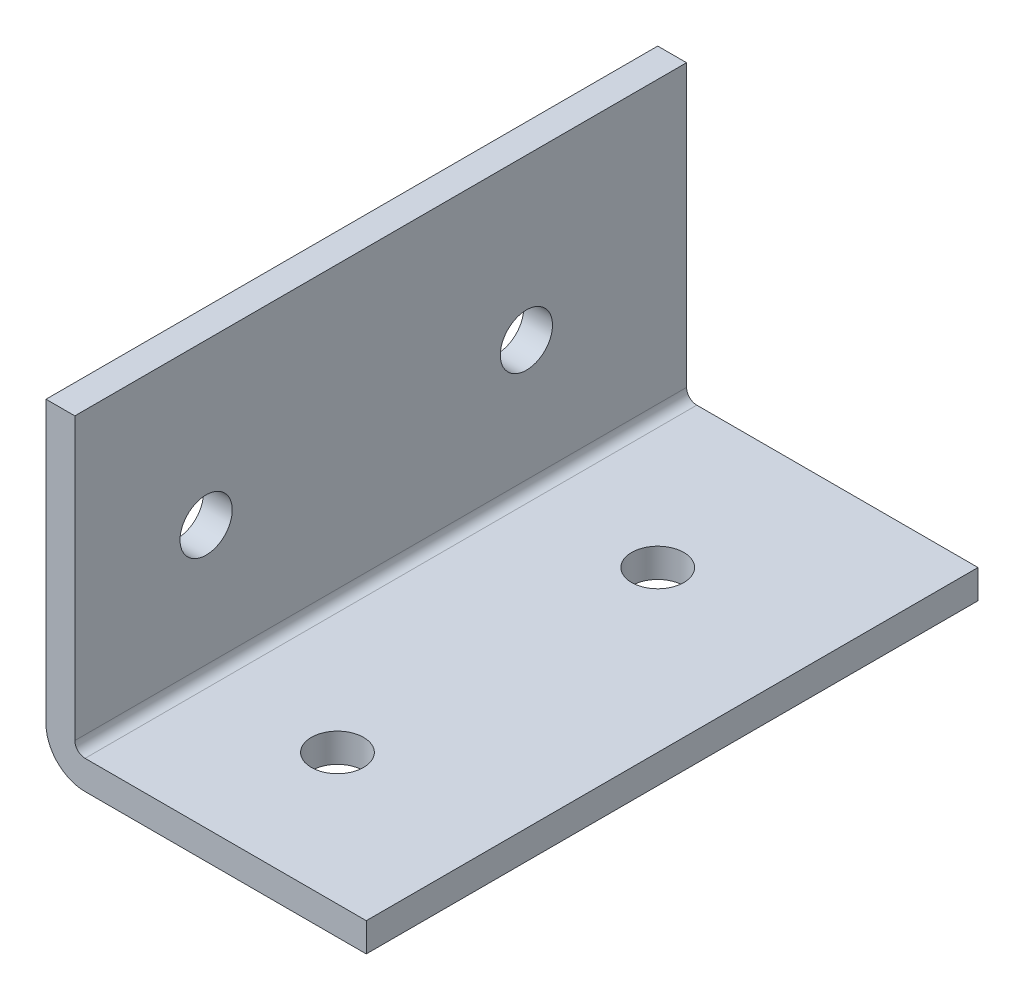
SolidWorks part; units mm, degrees
material "6061-T6 (SS)"
ref_plane "Front Plane" through (0, 0, 0) normal (0, 0, 1) x (1, 0, 0)
ref_plane "Top Plane" through (0, 0, 0) normal (0, 1, 0) x (1, 0, 0)
ref_plane "Right Plane" through (0, 0, 0) normal (1, 0, 0) x (0, 0, -1)
ref_plane "Plane1" through (0, 0, 0) normal (-1, 0, 0) x (0, -1, 0)
sketch "Sketch1" plane through (0, 0, 0) normal (-1, 0, 0) x (0, -1, 0)
  line L0 (0, 749.3) -> (-25.4, 749.3)
  line L1 (-25.4, 749.3) -> (-25.4, -749.3)
  line L2 (-25.4, -749.3) -> (0, -749.3)
  line L3 (0, -749.3) -> (0, 749.3)
extrude "Boss-Extrude1" add sketch "Sketch1" against normal blind 25.4
sketch "Sketch2" plane through (0, 0, -749.3) normal (0, 0, -1) x (-1, 0, 0)
  line L0 (-25.4, 2.286) -> (-2.286, 2.286)
  line L1 (-2.286, 2.286) -> (-2.286, 25.4)
  line L2 (-2.286, 25.4) -> (-25.4, 25.4)
  line L3 (-25.4, 25.4) -> (-25.4, 2.286)
extrude "Cut-Extrude1" cut sketch "Sketch2" against normal through all
hole_wizard "M3.5 Clearance Hole1" positions "Sketch4" profile "Sketch3" hole size "M3.5" standard "ANSI Metric"
sketch "Sketch4" plane through (0, 0, 0) normal (0, -1, 0) x (-1, 0, 0)
  point P0 (-12.7, 736.6)
  point P1 (-12.7, 711.2)
  point P2 (-12.7, 685.8)
  point P3 (-12.7, 660.4)
  point P4 (-12.7, 635)
  point P5 (-12.7, 609.6)
  point P6 (-12.7, 584.2)
  point P7 (-12.7, 558.8)
  point P8 (-12.7, 533.4)
  point P9 (-12.7, 508)
  point P10 (-12.7, 482.6)
  point P11 (-12.7, 457.2)
  point P12 (-12.7, 431.8)
  point P13 (-12.7, 406.4)
  point P14 (-12.7, 381)
  point P15 (-12.7, 355.6)
  point P16 (-12.7, 330.2)
  point P17 (-12.7, 304.8)
  point P18 (-12.7, 279.4)
  point P19 (-12.7, 254)
  point P20 (-12.7, 228.6)
  point P21 (-12.7, 203.2)
  point P22 (-12.7, 177.8)
  point P23 (-12.7, 152.4)
  point P24 (-12.7, 127)
  point P25 (-12.7, 101.6)
  point P26 (-12.7, 76.2)
  point P27 (-12.7, 50.8)
  point P28 (-12.7, 25.4)
  point P29 (-12.7, 0)
  point P30 (-12.7, -25.4)
  point P31 (-12.7, -50.8)
  point P32 (-12.7, -76.2)
  point P33 (-12.7, -101.6)
  point P34 (-12.7, -127)
  point P35 (-12.7, -152.4)
  point P36 (-12.7, -177.8)
  point P37 (-12.7, -203.2)
  point P38 (-12.7, -228.6)
  point P39 (-12.7, -254)
  point P40 (-12.7, -279.4)
  point P41 (-12.7, -304.8)
  point P42 (-12.7, -330.2)
  point P43 (-12.7, -355.6)
  point P44 (-12.7, -381)
  point P45 (-12.7, -406.4)
  point P46 (-12.7, -431.8)
  point P47 (-12.7, -457.2)
  point P48 (-12.7, -482.6)
  point P49 (-12.7, -508)
  point P50 (-12.7, -533.4)
  point P51 (-12.7, -558.8)
  point P52 (-12.7, -584.2)
  point P53 (-12.7, -609.6)
  point P54 (-12.7, -635)
  point P55 (-12.7, -660.4)
  point P56 (-12.7, -685.8)
  point P57 (-12.7, -711.2)
  point P58 (-12.7, -736.6)
sketch "Sketch3" plane through (12.7, 0, -736.6) normal (1, 0, 0) x (0, 0, -1)
  line L0 (0, 0) -> (0, 25.4)
  line L1 (0, 25.4) -> (2.0701, 25.4)
  line L2 (2.0701, 25.4) -> (2.0701, 0)
  line L5 (2.0701, 0) -> (0, 0)
  line L11 (0, -6.35) -> (0, 107.95) construction
  dimension "Thru Hole Dia." = 4.1402
  dimension "Thru Hole Depth" = 25.4
hole_wizard "M3.5 Clearance Hole2" positions "Sketch6" profile "Sketch5" hole size "M3.5" standard "ANSI Metric"
sketch "Sketch6" plane through (0, 0, 0) normal (-1, 0, 0) x (0, 0, 1)
  point P0 (711.2, 12.7)
  point P1 (736.6, 12.7)
  point P2 (685.8, 12.7)
  point P3 (660.4, 12.7)
  point P4 (635, 12.7)
  point P5 (609.6, 12.7)
  point P6 (584.2, 12.7)
  point P7 (558.8, 12.7)
  point P8 (533.4, 12.7)
  point P9 (508, 12.7)
  point P10 (482.6, 12.7)
  point P11 (457.2, 12.7)
  point P12 (431.8, 12.7)
  point P13 (406.4, 12.7)
  point P14 (381, 12.7)
  point P15 (355.6, 12.7)
  point P16 (330.2, 12.7)
  point P17 (304.8, 12.7)
  point P18 (279.4, 12.7)
  point P19 (254, 12.7)
  point P20 (228.6, 12.7)
  point P21 (203.2, 12.7)
  point P22 (177.8, 12.7)
  point P23 (152.4, 12.7)
  point P24 (127, 12.7)
  point P25 (101.6, 12.7)
  point P26 (76.2, 12.7)
  point P27 (50.8, 12.7)
  point P28 (25.4, 12.7)
  point P29 (0, 12.7)
  point P30 (-25.4, 12.7)
  point P31 (-50.8, 12.7)
  point P32 (-76.2, 12.7)
  point P33 (-101.6, 12.7)
  point P34 (-127, 12.7)
  point P35 (-152.4, 12.7)
  point P36 (-177.8, 12.7)
  point P37 (-203.2, 12.7)
  point P38 (-228.6, 12.7)
  point P39 (-254, 12.7)
  point P40 (-279.4, 12.7)
  point P41 (-304.8, 12.7)
  point P42 (-330.2, 12.7)
  point P43 (-355.6, 12.7)
  point P44 (-381, 12.7)
  point P45 (-406.4, 12.7)
  point P46 (-431.8, 12.7)
  point P47 (-457.2, 12.7)
  point P48 (-482.6, 12.7)
  point P49 (-508, 12.7)
  point P50 (-533.4, 12.7)
  point P51 (-558.8, 12.7)
  point P52 (-584.2, 12.7)
  point P53 (-609.6, 12.7)
  point P54 (-635, 12.7)
  point P55 (-660.4, 12.7)
  point P56 (-685.8, 12.7)
  point P57 (-711.2, 12.7)
  point P58 (-736.6, 12.7)
sketch "Sketch5" plane through (0, 12.7, 711.2) normal (0, 1, 0) x (0, 0, 1)
  line L0 (0, 0) -> (0, 25.4)
  line L1 (0, 25.4) -> (2.0701, 25.4)
  line L2 (2.0701, 25.4) -> (2.0701, 0)
  line L5 (2.0701, 0) -> (0, 0)
  line L11 (0, -6.35) -> (0, 107.95) construction
  dimension "Thru Hole Dia." = 4.1402
  dimension "Thru Hole Depth" = 25.4
chamfer "Chamfer1" distance 2.159 angle 45 4 edges at (25.4, 1.143, -749.3) (1.143, 25.4, -749.3) (1.143, 25.4, 749.3) (25.4, 1.143, 749.3)
fillet "Fillet1" radius 0.8128 1 edges at (2.286, 2.286, 0)
fillet "Fillet2" radius 3.0988 1 edges at (0, 0, 0)
sketch "Sketch8" plane through (0, 0, 749.3) normal (0, 0, 1) x (1, 0, 0)
  line L1 (-45.6555, -36.5704) -> (50.2275, -36.5704)
  line L2 (-45.6555, -36.5704) -> (-45.6555, 42.768)
  line L3 (-45.6555, 42.768) -> (50.2275, 42.768)
  line L4 (50.2275, -36.5704) -> (50.2275, 42.768)
  line L5 (-45.6555, -36.5704) -> (50.2275, 42.768) construction
  line L6 (-45.6555, 42.768) -> (50.2275, -36.5704) construction
  point P0 (2.286, 3.0988)
extrude "Cut-Extrude3" cut sketch "Sketch8" against normal blind 1371.6
sketch "Sketch9" plane through (0, 0, -749.3) normal (0, 0, -1) x (-1, 0, 0)
  line L1 (26.2815, -24.3339) -> (-30.643, -24.3339)
  line L2 (26.2815, -24.3339) -> (26.2815, 26.9489)
  line L3 (26.2815, 26.9489) -> (-30.643, 26.9489)
  line L4 (-30.643, -24.3339) -> (-30.643, 26.9489)
  line L5 (26.2815, -24.3339) -> (-30.643, 26.9489) construction
  line L6 (26.2815, 26.9489) -> (-30.643, -24.3339) construction
  point P0 (-2.1808, 1.3075)
extrude "Cut-Extrude4" cut sketch "Sketch9" against normal blind 76.2
sketch "Sketch11" plane through (0, 0, -622.3) normal (0, 0, 1) x (1, 0, 0)
  line L1 (-23.8761, -31.5895) -> (27.5864, -31.5895)
  line L2 (-23.8761, -31.5895) -> (-23.8761, 35.0872)
  line L3 (-23.8761, 35.0872) -> (27.5864, 35.0872)
  line L4 (27.5864, -31.5895) -> (27.5864, 35.0872)
  line L5 (-23.8761, -31.5895) -> (27.5864, 35.0872) construction
  line L6 (-23.8761, 35.0872) -> (27.5864, -31.5895) construction
  point P0 (1.8552, 1.7488)
extrude "Cut-Extrude6" cut sketch "Sketch11" against normal blind 2.286
